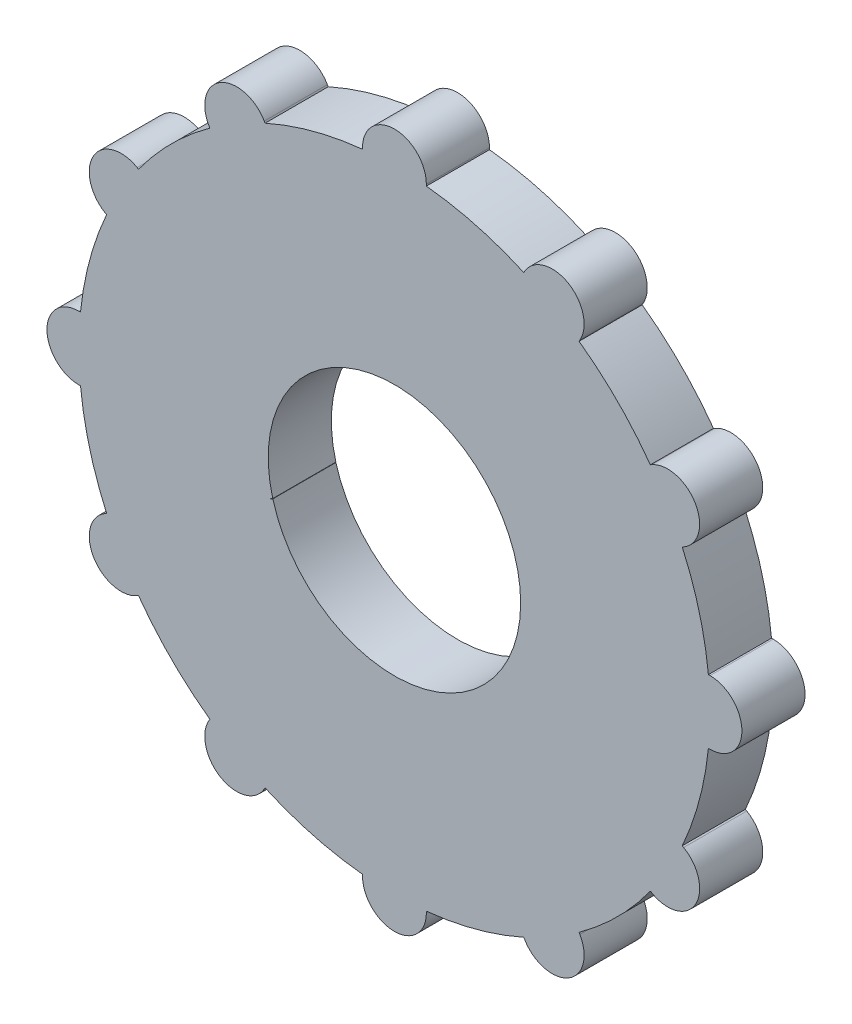
SolidWorks part; units mm, degrees
ref_plane "Front Plane" through (0, 0, 0) normal (0, 0, 1) x (1, 0, 0)
ref_plane "Top Plane" through (0, 0, 0) normal (0, 1, 0) x (1, 0, 0)
ref_plane "Right Plane" through (0, 0, 0) normal (1, 0, 0) x (0, 0, -1)
sketch "Sketch1" plane through (0, 0, 0) normal (0, 0, 1) x (1, 0, 0)
  line L0 (0, 20) -> (0, 50) construction
  line L1 (-5.0555, 49.7438) -> (-5.0555, 50)
  line L3 (10, 17.3205) -> (25, 43.3013) construction
  line L4 (20.4936, 45.6071) -> (20.6218, 45.829)
  line L5 (29.2501, 40.5516) -> (29.3782, 40.7735)
  line L6 (17.3205, 10) -> (43.3013, 25) construction
  line L7 (40.5516, 29.2501) -> (40.7735, 29.3782)
  line L8 (45.6071, 20.4936) -> (45.829, 20.6218)
  line L9 (20, 0) -> (50, 0) construction
  line L10 (49.7438, 5.0555) -> (50, 5.0555)
  line L11 (49.7438, -5.0555) -> (50, -5.0555)
  line L12 (17.3205, -10) -> (43.3013, -25) construction
  line L13 (45.6071, -20.4936) -> (45.829, -20.6218)
  line L14 (40.5516, -29.2501) -> (40.7735, -29.3782)
  line L15 (10, -17.3205) -> (25, -43.3013) construction
  line L18 (0, -20) -> (0, -50) construction
  line L20 (-5.0555, -49.7438) -> (-5.0555, -50)
  line L21 (-10, -17.3205) -> (-25, -43.3013) construction
  line L22 (-20.4936, -45.6071) -> (-20.6218, -45.829)
  line L23 (-29.2501, -40.5516) -> (-29.3782, -40.7735)
  line L24 (-17.3205, -10) -> (-43.3013, -25) construction
  line L26 (-19.8483, -5.6218) -> (-18.8676, -5.0555)
  line L27 (-20, 0) -> (-50, 0) construction
  line L28 (-49.7438, -5.0555) -> (-50, -5.0555)
  line L30 (-17.3205, 10) -> (-43.3013, 25) construction
  line L33 (-10, 17.3205) -> (-25, 43.3013) construction
  line L34 (-29.2501, 40.5516) -> (-29.3782, 40.7735)
  line L35 (-20.4936, 45.6071) -> (-20.6218, 45.829)
  line L48 (-45.6071, -20.4936) -> (-45.829, -20.6218)
  line L49 (-40.5516, -29.2501) -> (-40.7735, -29.3782)
  line L50 (-45.6071, 20.4936) -> (-45.829, 20.6218)
  line L51 (-40.5516, 29.2501) -> (-40.7735, 29.3782)
  line L55 (5.0555, -49.7438) -> (5.0555, -50)
  line L56 (20.4936, -45.6071) -> (20.6218, -45.829)
  line L57 (29.2501, -40.5516) -> (29.3782, -40.7735)
  line L58 (-49.7438, 5.0555) -> (-50, 5.0555)
  line L59 (5.0555, 49.7438) -> (5.0555, 50)
  circle A0 centre (0, 0) radius 20
  arc A2 (-45.6071, 20.4936) -> (-49.7438, 5.0555) centre (0, 0) ccw
  arc A4 (-5.0555, 20) -> (-5.015, 19.361) centre (0, 20) ccw
  arc A5 (5.0555, 50) -> (-5.0555, 50) centre (0, 50) ccw
  arc A6 (5.6218, 19.8483) -> (5.3374, 19.2747) centre (10, 17.3205) ccw
  arc A7 (29.3782, 40.7735) -> (20.6218, 45.829) centre (25, 43.3013) ccw
  arc A8 (14.7927, 14.3782) -> (14.2596, 14.0236) centre (17.3205, 10) ccw
  arc A9 (45.829, 20.6218) -> (40.7735, 29.3782) centre (43.3013, 25) ccw
  arc A10 (20, 5.0555) -> (19.361, 5.015) centre (20, 0) ccw
  arc A11 (50, -5.0555) -> (50, 5.0555) centre (50, 0) ccw
  arc A12 (19.8483, -5.6218) -> (19.2747, -5.3374) centre (17.3205, -10) ccw
  arc A13 (40.7735, -29.3782) -> (45.829, -20.6218) centre (43.3013, -25) ccw
  arc A14 (14.3782, -14.7927) -> (14.0236, -14.2596) centre (10, -17.3205) ccw
  arc A15 (20.6218, -45.829) -> (29.3782, -40.7735) centre (25, -43.3013) ccw
  arc A16 (5.0555, -20) -> (5.015, -19.361) centre (0, -20) ccw
  arc A17 (-5.0555, -50) -> (5.0555, -50) centre (0, -50) ccw
  arc A18 (-5.6218, -19.8483) -> (-5.3374, -19.2747) centre (-10, -17.3205) ccw
  arc A19 (-29.3782, -40.7735) -> (-20.6218, -45.829) centre (-25, -43.3013) ccw
  arc A20 (-14.7927, -14.3782) -> (-14.2596, -14.0236) centre (-17.3205, -10) ccw
  arc A21 (-45.829, -20.6218) -> (-40.7735, -29.3782) centre (-43.3013, -25) ccw
  arc A22 (-20, -5.0555) -> (-19.361, -5.015) centre (-20, 0) ccw
  arc A23 (-50, 5.0555) -> (-50, -5.0555) centre (-50, 0) ccw
  arc A24 (-19.8483, 5.6218) -> (-19.2747, 5.3374) centre (-17.3205, 10) ccw
  arc A25 (-40.7735, 29.3782) -> (-45.829, 20.6218) centre (-43.3013, 25) ccw
  arc A26 (-14.3782, 14.7927) -> (-14.0236, 14.2596) centre (-10, 17.3205) ccw
  arc A27 (-20.6218, 45.829) -> (-29.3782, 40.7735) centre (-25, 43.3013) ccw
  arc A28 (-14.2596, 14.0236) -> (-14.7927, 14.3782) centre (-17.3205, 10) ccw
  arc A31 (-19.361, 5.015) -> (-20, 5.0555) centre (-20, 0) ccw
  arc A34 (-19.2747, -5.3374) -> (-19.8483, -5.6218) centre (-17.3205, -10) ccw
  arc A37 (-14.0236, -14.2596) -> (-14.3782, -14.7927) centre (-10, -17.3205) ccw
  arc A40 (40.5516, 29.2501) -> (29.2501, 40.5516) centre (0, 0) ccw
  arc A41 (-5.3374, 19.2747) -> (-5.6218, 19.8483) centre (-10, 17.3205) ccw
  arc A44 (5.015, 19.361) -> (5.0555, 20) centre (0, 20) ccw
  arc A45 (14.0236, 14.2596) -> (14.3782, 14.7927) centre (10, 17.3205) ccw
  arc A46 (19.2747, 5.3374) -> (19.8483, 5.6218) centre (17.3205, 10) ccw
  arc A47 (19.361, -5.015) -> (20, -5.0555) centre (20, 0) ccw
  arc A48 (14.2596, -14.0236) -> (14.7927, -14.3782) centre (17.3205, -10) ccw
  arc A49 (5.3374, -19.2747) -> (5.6218, -19.8483) centre (10, -17.3205) ccw
  arc A50 (-5.015, -19.361) -> (-5.0555, -20) centre (0, -20) ccw
  arc A51 (29.2501, -40.5516) -> (40.5516, -29.2501) centre (0, 0) ccw
  arc A52 (5.0555, -49.7438) -> (20.4936, -45.6071) centre (0, 0) ccw
  arc A53 (-20.4936, -45.6071) -> (-5.0555, -49.7438) centre (0, 0) ccw
  arc A54 (-49.7438, -5.0555) -> (-45.6071, -20.4936) centre (0, 0) ccw
  arc A55 (-5.0555, 49.7438) -> (-20.4936, 45.6071) centre (0, 0) ccw
  arc A56 (-40.5516, -29.2501) -> (-29.2501, -40.5516) centre (0, 0) ccw
  arc A57 (20.4936, 45.6071) -> (5.0555, 49.7438) centre (0, 0) ccw
  arc A58 (49.7438, 5.0555) -> (45.6071, 20.4936) centre (0, 0) ccw
  arc A59 (45.6071, -20.4936) -> (49.7438, -5.0555) centre (0, 0) ccw
  arc A60 (-29.2501, 40.5516) -> (-40.5516, 29.2501) centre (0, 0) ccw
  point P8 (0, 35)
  point P17 (17.5, 30.3109)
  point P24 (30.3109, 17.5)
  point P31 (35, 0)
  point P38 (30.3109, -17.5)
  point P45 (17.5, -30.3109)
  point P52 (0, -35)
  point P59 (-17.5, -30.3109)
  point P66 (-30.3109, -17.5)
  point P73 (-35, 0)
  point P80 (-30.3109, 17.5)
  point P87 (-17.5, 30.3109)
  point P92 (0, 0)
  point P93 (-30.3109, 17.5)
  point P104 (-35, 0)
  point P113 (-30.3109, -17.5)
  point P122 (-17.5, -30.3109)
  point P138 (-17.5, 30.3109)
extrude "Boss-Extrude1" add sketch "Sketch1" along normal blind 10 contours L34 A60 L51 A25 L50 A2 L58 A23 L28 A54 L48 A21 L49 A56 L23 A19 L22 A53 L20 A17 L55 A52 L56 A15 L57 A51 L14 A13 L13 A59 L11 A11 L10 A58 L8 A9 L7 A40 L5 A7 L4 A57 L59 A5 L1 A55 L35 A27 A0 A34
